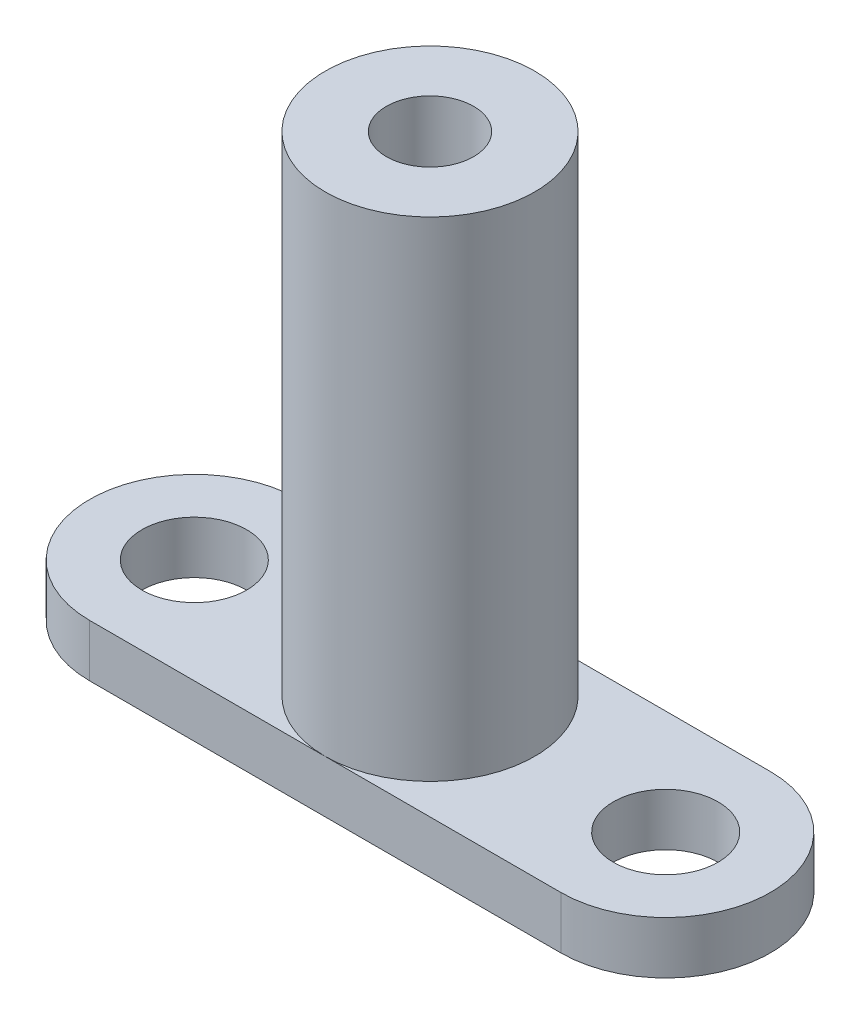
SolidWorks part; units mm, degrees
ref_plane "前视基准面" through (0, 0, 0) normal (0, 0, 1) x (1, 0, 0)
ref_plane "上视基准面" through (0, 0, 0) normal (0, 1, 0) x (1, 0, 0)
ref_plane "右视基准面" through (0, 0, 0) normal (1, 0, 0) x (0, 0, -1)
sketch "草图1" plane through (0, 0, 0) normal (0, 1, 0) x (1, 0, 0)
  line L0 (-13.5, 6) -> (13.5, 6)
  line L1 (-13.5, -6) -> (13.5, -6)
  circle A0 centre (-13.5, 0) radius 6
  circle A1 centre (13.5, 0) radius 6
  dimension "D1" = 12
  dimension "D2" = 13.5
  dimension "D3" = 13.5
extrude "凸台-拉伸1" add sketch "草图1" along normal blind 3 contours A0 | A1 L0 A0 L1 | A1
sketch "草图2" plane through (0, 3, 0) normal (0, 1, 0) x (1, 0, 0)
  circle A0 centre (0, 0) radius 6
extrude "凸台-拉伸2" add sketch "草图2" along normal blind 28
hole_wizard "M6 螺纹孔1" positions "草图3" profile "草图5" tap size "M6" standard "GB"
sketch "草图3" plane through (0, 31, 0) normal (0, 1, 0) x (1, 0, 0)
  point P0 (0, 0)
cosmetic thread "孔螺蚊线1"
sketch "草图5" plane through (0, 31, 0) normal (1, 0, 0) x (0, 0, 1)
  line L0 (0, 0) -> (0, 13.5022)
  line L1 (0, 13.5022) -> (2.5, 12)
  line L2 (2.5, 12) -> (2.5, 0)
  line L5 (2.5, 0) -> (0, 0)
  line L10 (0, 13.5022) -> (-2.5, 12) construction
  line L11 (0, -6.35) -> (0, 107.95) construction
  dimension "螺纹孔钻头直径" = 5
  dimension "螺纹孔钻头深度" = 12
  dimension "导头角度" = 118
sketch "草图6" plane through (0, 3, 0) normal (0, 1, 0) x (1, 0, 0)
  circle A0 centre (-13.5, 0) radius 3
  circle A1 centre (13.5, 0) radius 3
  dimension "D1" = 6
  dimension "D2" = 6
extrude "切除-拉伸1" cut sketch "草图6" against normal blind 10
